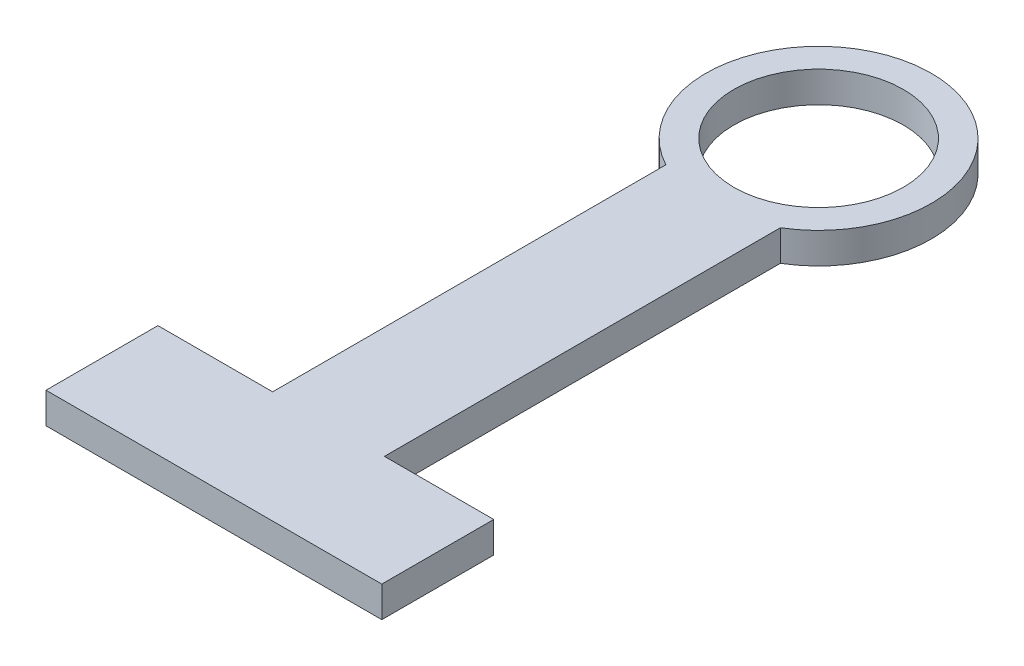
SolidWorks part; units mm, degrees
ref_plane "Front Plane" through (0, 0, 0) normal (0, 0, 1) x (1, 0, 0)
ref_plane "Top Plane" through (0, 0, 0) normal (0, 1, 0) x (1, 0, 0)
ref_plane "Right Plane" through (0, 0, 0) normal (1, 0, 0) x (0, 0, -1)
sketch "Sketch1" plane through (0, 0, 0) normal (0, 1, 0) x (1, 0, 0)
  line L0 (-12.1314, -20.0181) -> (13.2313, -20.0181)
  line L1 (13.2313, -20.0181) -> (13.2313, -111.76)
  line L2 (13.2313, -111.76) -> (38.0361, -111.76)
  line L3 (38.0361, -111.76) -> (38.0361, -137.16)
  line L4 (38.0361, -137.16) -> (-38.1639, -137.16)
  line L5 (-38.1639, -137.16) -> (-38.1639, -111.76)
  line L6 (-38.1639, -111.76) -> (-12.1314, -111.76)
  line L7 (-12.1314, -111.76) -> (-12.1314, -20.0181)
  circle A0 centre (0, 0) radius 19.2405
  circle A1 centre (0, 0) radius 25.5905
  dimension "D1" = 38.481
  dimension "D2" = 6.35
  dimension "D3" = 137.16
  dimension "D5" = 25.4
  dimension "D6" = 76.2
extrude "Boss-Extrude1" add sketch "Sketch1" along normal blind 7 contours A1 L0 L7 L6 L5 L4 L3 L2 L1 | L0 A1 A0 | L0 A1
